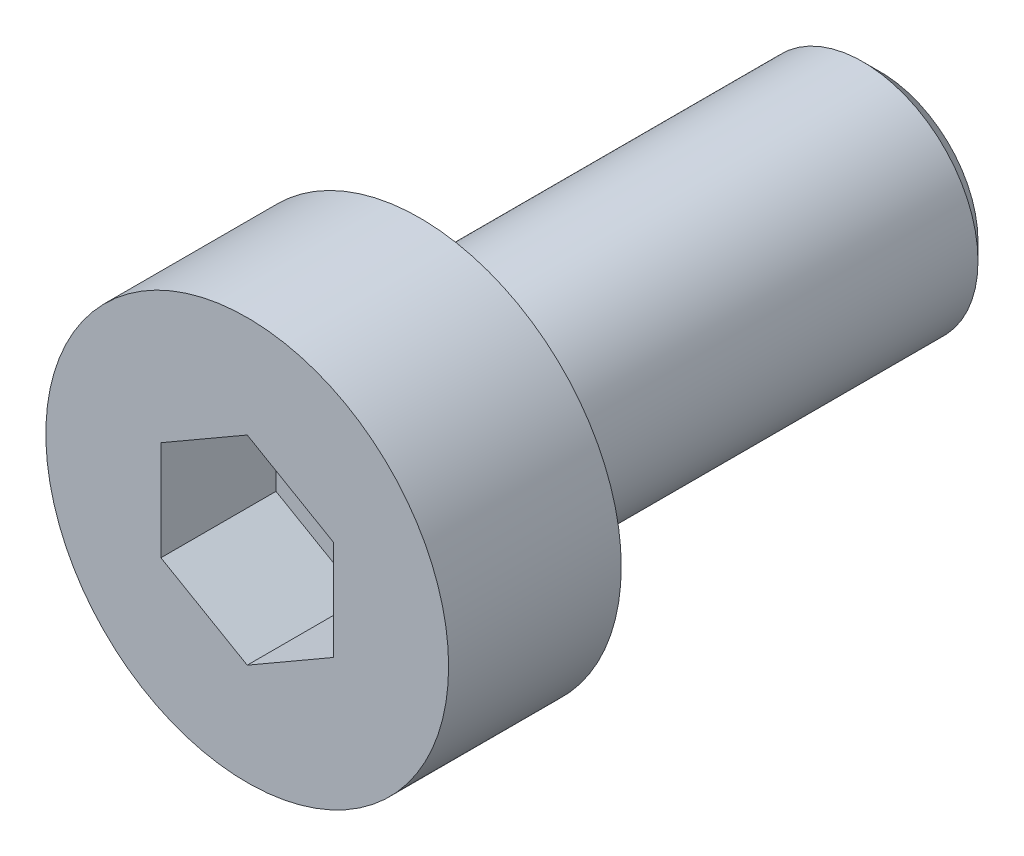
SolidWorks part; units mm, degrees
ref_plane "Front Plane" through (0, 0, 0) normal (0, 0, 1) x (1, 0, 0)
ref_plane "Top Plane" through (0, 0, 0) normal (0, 1, 0) x (1, 0, 0)
ref_plane "Right Plane" through (0, 0, 0) normal (1, 0, 0) x (0, 0, -1)
sketch "Sketch1" plane through (0, 0, 0) normal (0, 0, 1) x (1, 0, 0)
  circle A0 centre (0, 0) radius 3.5
  dimension "D1" = 7
extrude "Boss-Extrude1" add sketch "Sketch1" along normal blind 3
sketch "Sketch2" plane through (0, 0, 0) normal (0, 0, -1) x (-1, 0, 0)
  circle A0 centre (0, 0) radius 2
  dimension "D1" = 4
extrude "Boss-Extrude2" add sketch "Sketch2" along normal blind 8
chamfer "Chamfer1" distance 0.3 angle 45 1 edges at (-2, 0, -8)
sketch "Sketch3" plane through (0, 0, 3) normal (0, 0, 1) x (1, 0, 0)
  line L1 (0, 1.7321) -> (-1.5, 0.866)
  line L2 (-1.5, 0.866) -> (-1.5, -0.866)
  line L3 (-1.5, -0.866) -> (0, -1.7321)
  line L4 (0, -1.7321) -> (1.5, -0.866)
  line L5 (1.5, -0.866) -> (1.5, 0.866)
  line L6 (1.5, 0.866) -> (0, 1.7321)
  circle A0 centre (0, 0) radius 1.5 construction
  dimension "D1" = 3
extrude "Cut-Extrude1" cut sketch "Sketch3" against normal blind 2
